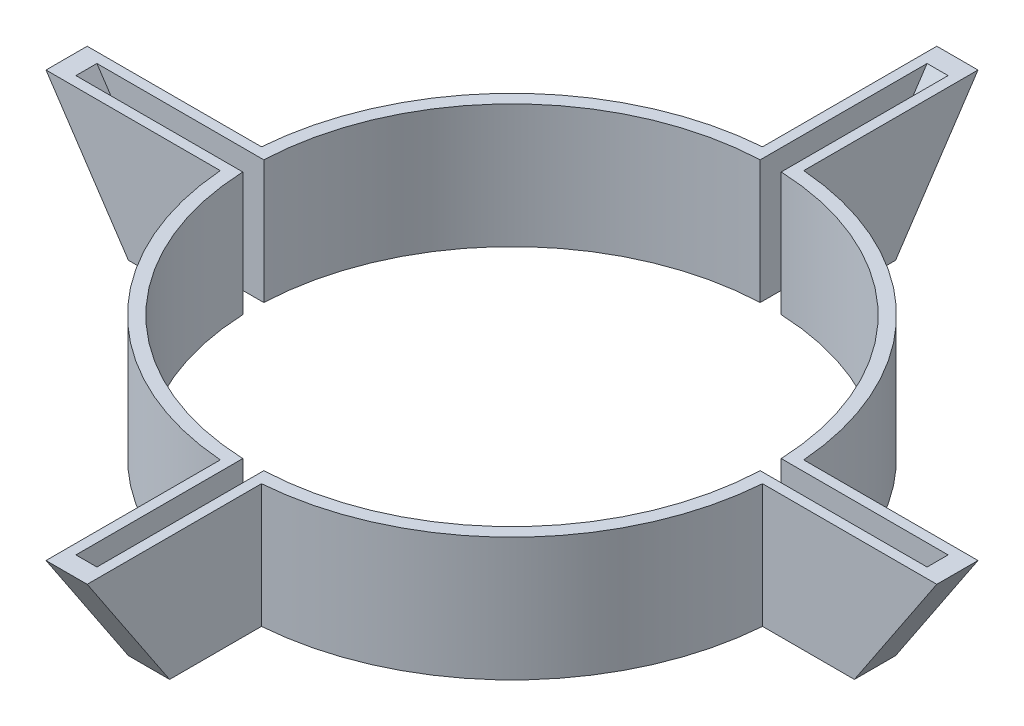
SolidWorks part; units mm, degrees
ref_plane "Front Plane" through (0, 0, 0) normal (0, 0, 1) x (1, 0, 0)
ref_plane "Top Plane" through (0, 0, 0) normal (0, 1, 0) x (1, 0, 0)
ref_plane "Right Plane" through (0, 0, 0) normal (1, 0, 0) x (0, 0, -1)
sketch "Sketch1" plane through (0, 0, 0) normal (0, 1, 0) x (1, 0, 0)
  circle A0 centre (0, 0) radius 39.9034
  circle A1 centre (0, 0) radius 41.9034
  dimension "D1" = 79.8068
  dimension "D2" = 2
extrude "Boss-Extrude1" add sketch "Sketch1" along normal mid plane 114.3
sketch "Sketch2" plane through (0, 0, 0) normal (1, 0, 0) x (0, 0, -1)
  line L0 (41.9034, 57.15) -> (41.9034, -44.45) construction
  line L1 (41.9034, -57.15) -> (41.9034, 57.15) construction
  line L2 (41.9034, 57.15) -> (109.6366, 57.15) construction
  line L3 (109.6366, 57.15) -> (41.9034, -44.45) construction
  dimension "D1" = 101.6
  dimension "D2" = 33.69
ref_plane "Plane1" through (0, -44.45, -41.9034) normal (0, 0, -1) x (-1, 0, 0)
sketch "Sketch3" plane through (0, -44.45, -41.9034) normal (0, 0, -1) x (-1, 0, 0)
  line L0 (-10.0825, 0) -> (10.0825, 0) construction
  point P3 (0, 0)
ref_plane "Plane2" through (0, -33.0169, -49.5255) normal (0, 0.5547, 0.8321) x (1, 0, 0)
sketch "Sketch4" plane through (0, -33.0169, -49.5255) normal (0, 0.5547, 0.8321) x (1, 0, 0)
  line L0 (3.175, -13.7409) -> (-3.175, -13.7409)
  line L1 (-3.175, -13.7409) -> (-3.175, 82.967)
  line L2 (-3.175, 82.967) -> (3.175, 82.967)
  line L3 (3.175, 82.967) -> (3.175, -13.7409)
  point P4 (0, -13.7409)
  dimension "D1" = 6.35
  dimension "D2" = 25.4
extrude "Boss-Extrude2" add sketch "Sketch4" along normal up to surface (64.6165 mm away)
sketch "Sketch5" plane through (0, 69.0328, -46.0217) normal (0, 0.8321, -0.5547) x (1, 0, 0)
  line L0 (0, 3.1647) -> (0, 59.5221) construction
  line L1 (-1.6192, -10.1336) -> (1.6193, -10.1336)
  line L2 (-1.6192, -10.1336) -> (-1.6192, 56.9821)
  line L3 (-1.6192, 56.9821) -> (1.6193, 56.9821)
  line L4 (1.6193, -10.1336) -> (1.6193, 56.9821)
  line L5 (-1.6192, -10.1336) -> (1.6193, 56.9821) construction
  line L6 (-1.6192, 56.9821) -> (1.6193, -10.1336) construction
  line L7 (3.175, 59.5221) -> (-3.175, 59.5221) construction
  point P0 (0, 23.4243)
  dimension "D1" = 3.2385
  dimension "D2" = 2.54
extrude "Cut-Extrude1" cut sketch "Sketch5" against normal up to surface (9.7384 mm away)
pattern_circular "CirPattern1" count 4 over 360 about axis through (0, 0, 0) along (0, 1, 0) of "Cut-Extrude1", "Boss-Extrude2"
sketch "Sketch6" plane through (0, 0, 0) normal (1, 0, 0) x (0, 0, -1)
  line L1 (95.5472, 71.8587) -> (-95.5472, 71.8587)
  line L2 (95.5472, 71.8587) -> (95.5472, -4.3413)
  line L3 (95.5472, -4.3413) -> (-95.5472, -4.3413)
  line L4 (-95.5472, 71.8587) -> (-95.5472, -4.3413)
  line L5 (95.5472, -80.5413) -> (-95.5472, -80.5413)
  line L6 (95.5472, -80.5413) -> (95.5472, -23.3913)
  line L7 (95.5472, -23.3913) -> (-95.5472, -23.3913)
  line L8 (-95.5472, -80.5413) -> (-95.5472, -23.3913)
  dimension "D1" = 19.05
  dimension "D2" = 57.15
  dimension "D3" = 76.2
extrude "Cut-Extrude2" cut sketch "Sketch6" against normal through all both and the other way through all
